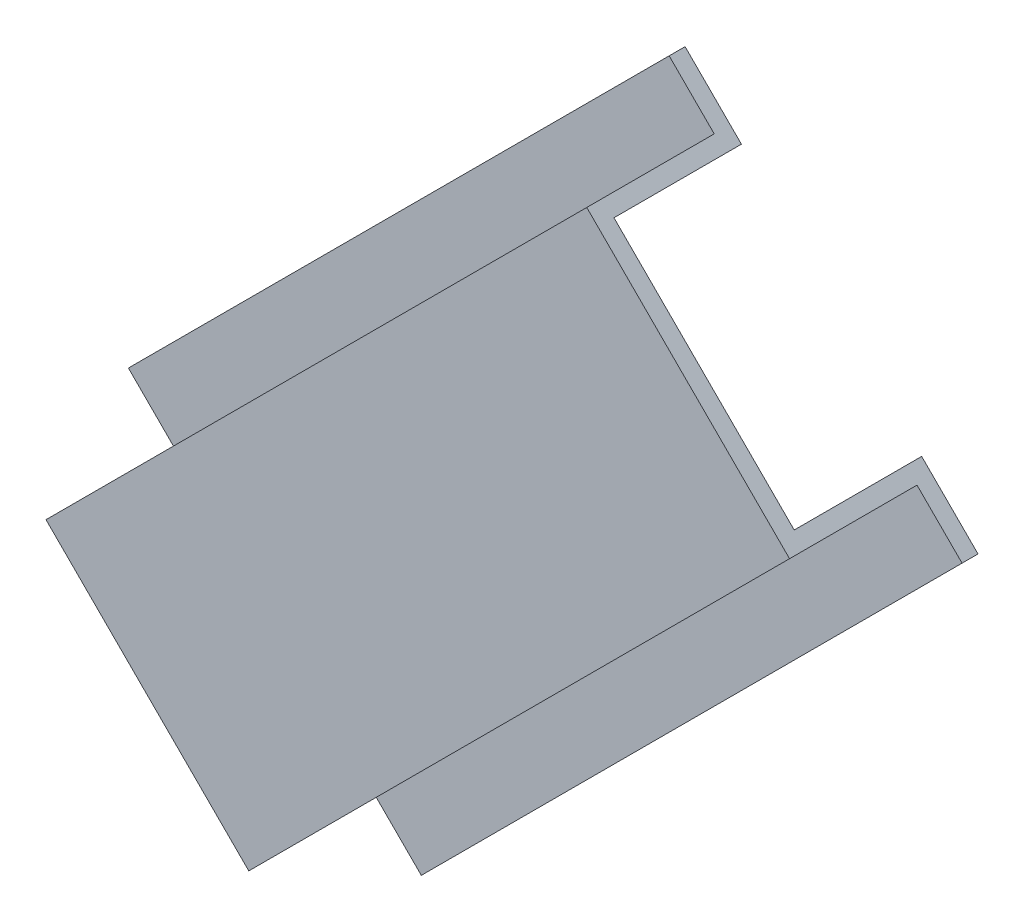
SolidWorks part; units mm, degrees
ref_plane "Front Plane" through (0, 0, 0) normal (0, 0, 1) x (1, 0, 0)
ref_plane "Top Plane" through (0, 0, 0) normal (0, 1, 0) x (1, 0, 0)
ref_plane "Right Plane" through (0, 0, 0) normal (1, 0, 0) x (0, 0, -1)
sketch "Sketch2" plane through (-53.8815, -53.8815, 0) normal (-0.7071, -0.7071, 0) x (0, 0, 1)
  line L0 (3.175, -28.575) -> (28.575, -28.575)
  line L1 (0, -25.4) -> (25.4, -25.4)
  line L2 (0, -25.4) -> (0, -41.275)
  line L3 (3.175, 28.575) -> (28.575, 28.575)
  line L4 (25.4, -25.4) -> (25.4, 25.4)
  line L5 (28.575, -28.575) -> (28.575, 28.575)
  line L6 (0, 0) -> (36.0732, 0) construction
  line L8 (-3.175, -28.575) -> (-3.175, 28.575) construction
  line L9 (0, -25.4) -> (0, 25.4) construction
  line L10 (0, -41.275) -> (3.175, -41.275)
  line L11 (3.175, -41.275) -> (3.175, -28.575)
  line L12 (-3.175, -28.575) -> (28.575, -28.575) construction
  line L13 (-3.175, 28.575) -> (28.575, 28.575) construction
  line L14 (25.4, -25.4) -> (25.4, 25.4) construction
  line L15 (28.575, -28.575) -> (28.575, 28.575) construction
  line L16 (0, 25.4) -> (25.4, 25.4) construction
  line L17 (0, 25.4) -> (25.4, 25.4)
  line L18 (3.175, 41.275) -> (3.175, 28.575)
  line L19 (0, 41.275) -> (3.175, 41.275)
  line L20 (0, 25.4) -> (0, 41.275)
  point P12 (28.575, 0)
  point P19 (25.4, 0)
  dimension "D1" = 25.4
  dimension "D2" = 12.7
  dimension "D3" = 3.175
  dimension "D4" = 3.175
extrude "Boss-Extrude1" add sketch "Sketch2" against normal blind 152.4
